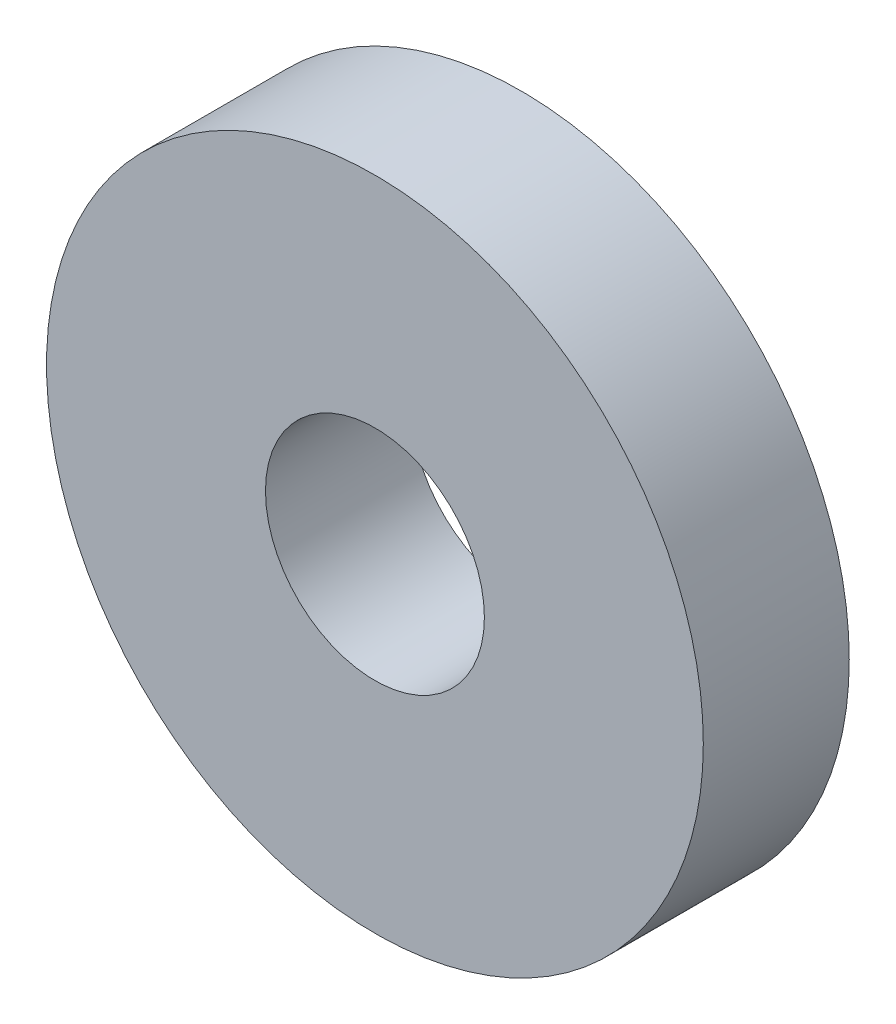
SolidWorks part; units mm, degrees
ref_plane "Front Plane" through (0, 0, 0) normal (0, 0, 1) x (1, 0, 0)
ref_plane "Top Plane" through (0, 0, 0) normal (0, 1, 0) x (1, 0, 0)
ref_plane "Right Plane" through (0, 0, 0) normal (1, 0, 0) x (0, 0, -1)
sketch "Sketch1" plane through (0, 0, 0) normal (0, 0, 1) x (1, 0, 0)
  circle A0 centre (0, 0) radius 4.5
  circle A1 centre (0, 0) radius 1.5
  dimension "D1" = 3
  dimension "D2" = 9
extrude "Boss-Extrude1" add sketch "Sketch1" along normal blind 2
